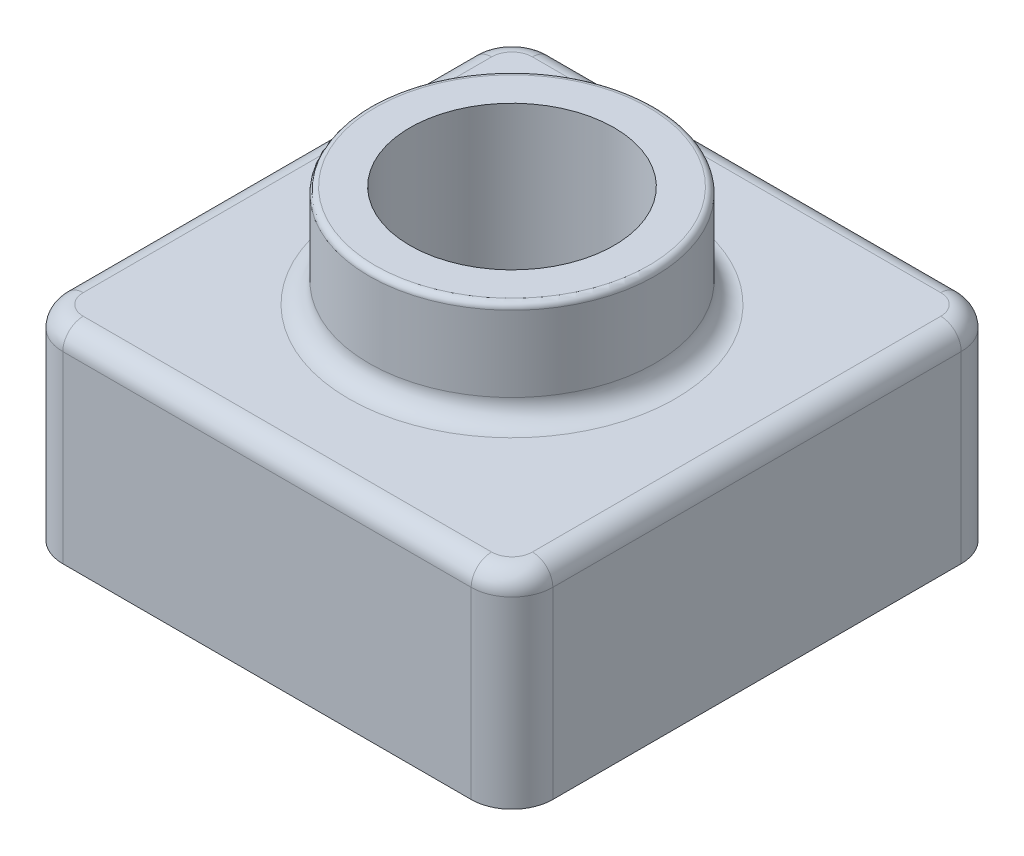
SolidWorks part; units mm, degrees
material "Chrome Stainless Steel"
ref_plane "Front Plane" through (0, 0, 0) normal (0, 0, 1) x (1, 0, 0)
ref_plane "Top Plane" through (0, 0, 0) normal (0, 1, 0) x (1, 0, 0)
ref_plane "Right Plane" through (0, 0, 0) normal (1, 0, 0) x (0, 0, -1)
sketch "Sketch1" plane through (0, 0, 0) normal (0, 1, 0) x (1, 0, 0)
  line L1 (-47.6196, 39.1626) -> (72.3804, 39.1626)
  line L2 (-47.6196, 39.1626) -> (-47.6196, -80.8374)
  line L3 (-47.6196, -80.8374) -> (72.3804, -80.8374)
  line L4 (72.3804, 39.1626) -> (72.3804, -80.8374)
  dimension "D1" = 120
  dimension "D2" = 120
extrude "Boss-Extrude1" add sketch "Sketch1" along normal blind 50 contours L1 L4 L3 L2
sketch "Sketch2" plane through (0, 50, 0) normal (0, 1, 0) x (1, 0, 0)
  line L0 (-47.6196, 39.1626) -> (-47.6196, -80.8374) construction
  line L1 (-47.6196, -80.8374) -> (72.3804, -80.8374) construction
  circle A0 centre (12.3804, -20.8374) radius 35
  dimension "D1" = 70
  dimension "D2" = 60
  dimension "D3" = 60
sketch "Sketch3" plane through (0, 50, 0) normal (0, 1, 0) x (1, 0, 0)
extrude "Boss-Extrude2" add sketch "Sketch2" along normal blind 25 contours A0
sketch "Sketch4" plane through (0, 75, 0) normal (0, 1, 0) x (1, 0, 0)
  circle A0 centre (12.3804, -20.8374) radius 25
  dimension "D1" = 50
extrude "Cut-Extrude4" cut sketch "Sketch4" against normal through all contours A0
fillet "Fillet3" radius 10 4 edges at (-47.6196, 25, 80.8374) (-47.6196, 25, -39.1626) (72.3804, 25, 80.8374) (72.3804, 25, -39.1626)
fillet "Fillet5" radius 1.5 1 edges at (12.3804, 75, 55.8374)
fillet "Fillet6" radius 5 9 edges at (-44.6907, 50, -36.2336) (12.3804, 50, -39.1626) (69.4515, 50, -36.2336) (72.3804, 50, 20.8374) (69.4515, 50, 77.9085) (12.3804, 50, 80.8374) (-44.6907, 50, 77.9085) (-47.6196, 50, 20.8374) (12.3804, 50, 55.8374)
shell "Shell3" thickness 2
